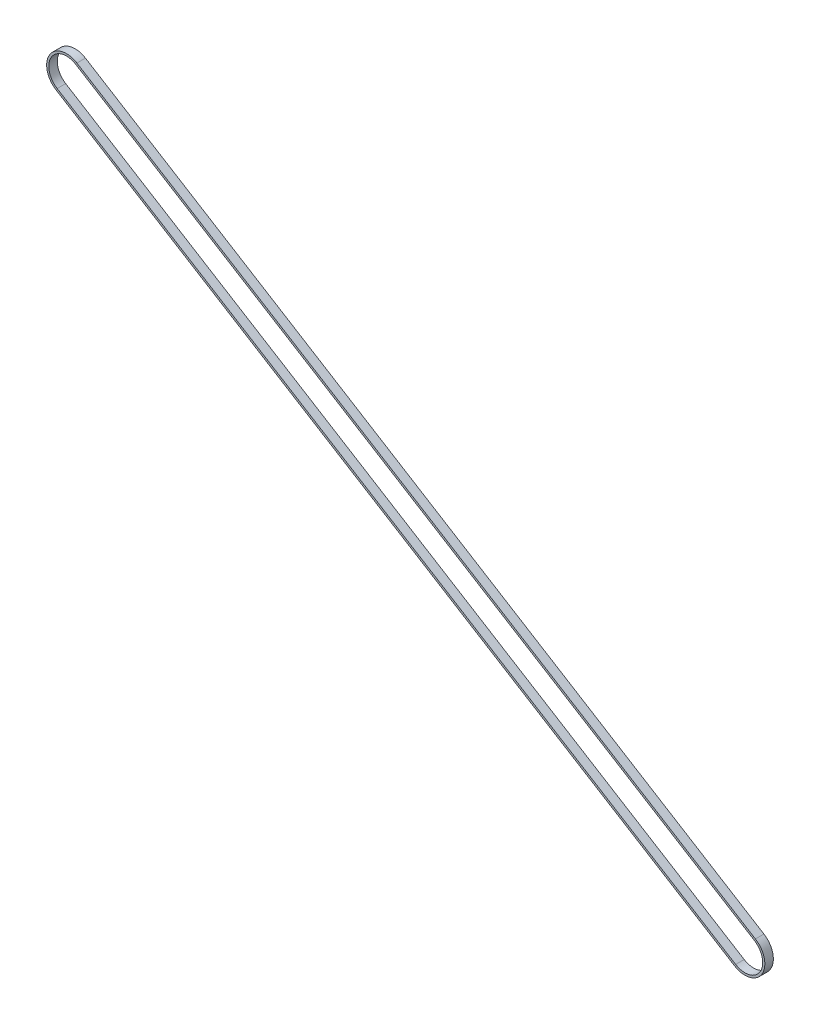
SolidWorks part; units mm, degrees
ref_plane "前视基准面" through (0, 0, 0) normal (0, 0, 1) x (1, 0, 0)
ref_plane "上视基准面" through (0, 0, 0) normal (0, 1, 0) x (1, 0, 0)
ref_plane "右视基准面" through (0, 0, 0) normal (1, 0, 0) x (0, 0, -1)
sketch "草图2" plane through (0, 0, 0) normal (0, 0, 1) x (1, 0, 0)
  line L0 (0, 0) -> (1, 0) construction
  line L1 (0, 0) -> (0, 1) construction
  line L2 (-6.5583, -10.612) -> (-484.4777, 284.7433)
  line L3 (-471.3612, 305.9673) -> (6.5583, 10.612)
  arc A0 (6.5583, 10.612) -> (-6.5583, -10.612) centre (0, 0) cw
  arc A1 (-484.4777, 284.7433) -> (-471.3612, 305.9673) centre (-477.9194, 295.3553) cw
extrude "拉伸-薄壁1" add sketch "草图2" along normal blind 6 thin thin type one direction wall 1.5
